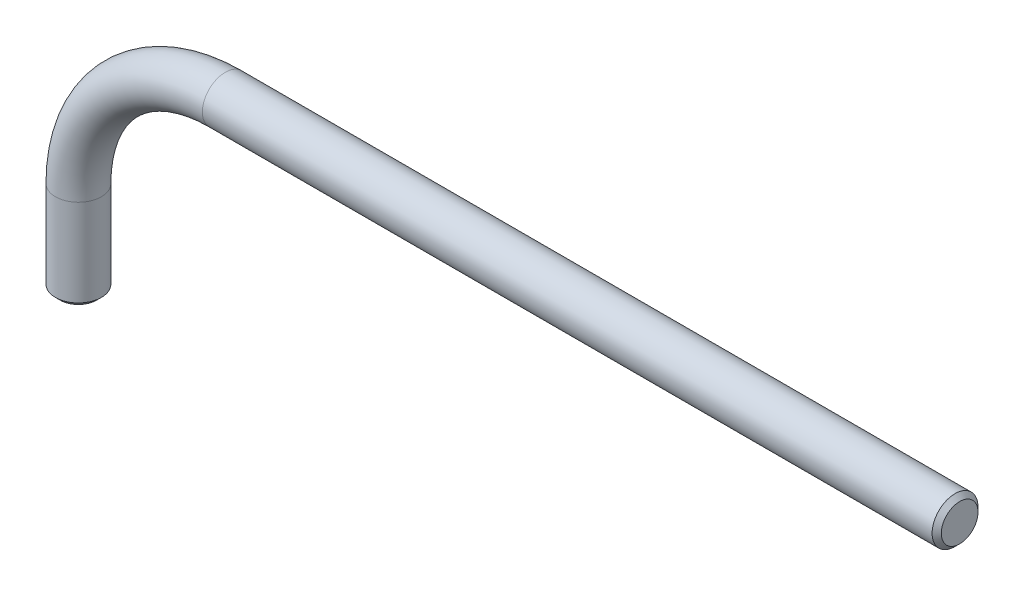
SolidWorks part; units mm, degrees
material "Plain Carbon Steel"
ref_plane "Front Plane" through (0, 0, 0) normal (0, 0, 1) x (1, 0, 0)
ref_plane "Top Plane" through (0, 0, 0) normal (0, 1, 0) x (1, 0, 0)
ref_plane "Right Plane" through (0, 0, 0) normal (1, 0, 0) x (0, 0, -1)
sketch "Sketch1" plane through (0, 0, 0) normal (0, 0, 1) x (1, 0, 0)
  line L0 (0, 0) -> (-80, 0)
  line L1 (-96, -16) -> (-96, -26)
  arc A0 (-80, 0) -> (-96, -16) centre (-80, -16) ccw
  point P6 (-96, 0)
  dimension "D3" = 16
  dimension "D1" = 96
  dimension "D2" = 26
sweep "Sweep1" add path "Sketch1" circular profile diameter 5 parameters "D3"=5
chamfer "Chamfer1" distance 0.5 angle 45 2 edges at (0, 0, 2.5) (-96, -26, 2.5)
